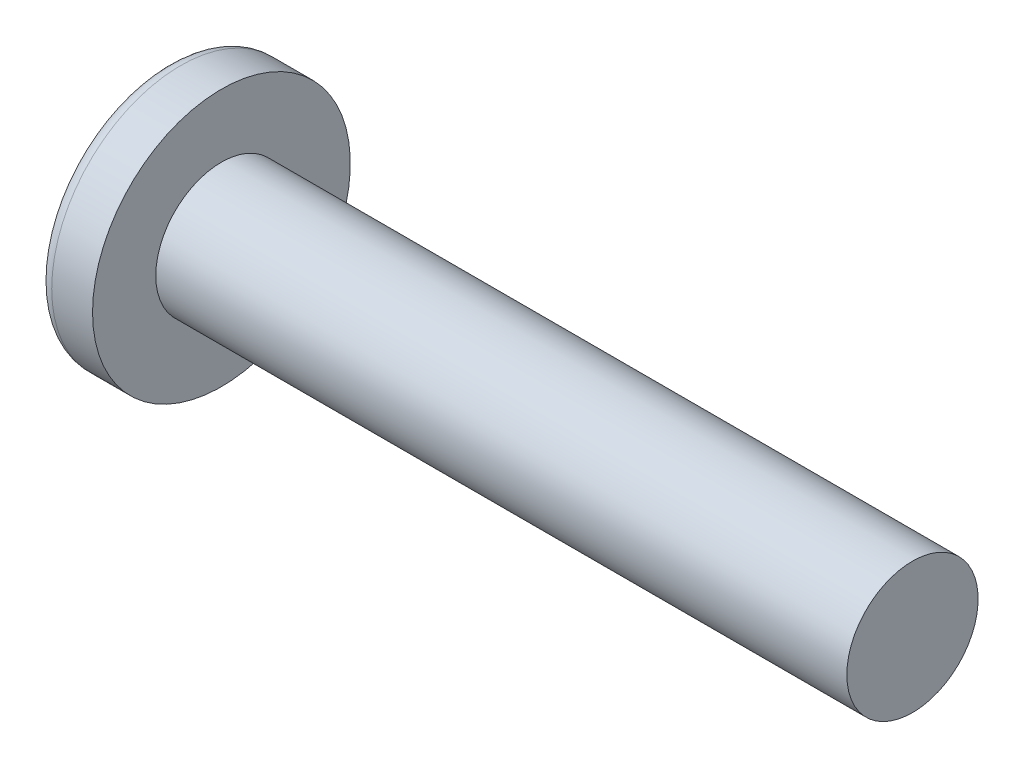
SolidWorks part; units mm, degrees
ref_plane "Plane1" through (0, 0, 0) normal (0, 0, 1) x (1, 0, 0)
ref_plane "Plane2" through (0, 0, 0) normal (0, 1, 0) x (1, 0, 0)
ref_plane "Plane3" through (0, 0, 0) normal (1, 0, 0) x (0, 0, -1)
sketch "BodySke" plane through (0, 0, 0) normal (0, 0, 1) x (1, 0, 0)
  line L0 (3.3782, 2.413) -> (3.3782, 4.7371)
  line L1 (3.9078, 6.35) -> (3.9078, -3.175) construction
  line L2 (-25.4, 0) -> (127, 0) construction
  line L3 (28.7782, 0) -> (0, 0)
  line L4 (3.3782, 2.413) -> (28.7782, 2.413)
  line L5 (28.7782, 2.413) -> (28.7782, 0)
  line L6 (1.8777, 4.7371) -> (3.3782, 4.7371)
  line L7 (3.3782, -2.413) -> (28.7782, -2.413) construction
  line L8 (3.3782, 6.35) -> (3.3782, -3.175) construction
  arc A0 (1.4662, 4.5269) -> (0, 0) centre (7.7216, 0) ccw
  arc A2 (1.4662, 4.5269) -> (1.8777, 4.7371) centre (1.8777, 4.2291) cw
  dimension "Head_crown_rad" = 7.7216
  dimension "Head_fillet_rad" = 0.508
  dimension "Diameter" = 4.826
  dimension "Length" = 25.4
  dimension "Head_ht" = 3.3782
  dimension "Head_dia" = 9.4742
  dimension "Advance" = 1.0592
  dimension "Thread_nom" = 25.4
revolve "Base-Revolve" add sketch "BodySke" angle 360 about L2
cosmetic thread "ThreadCosmetic" [suppressed] parameters "Thread_length"=24.3408, "Thread_minor"=3.5662
sketch "Sketch3" plane through (0, 0, 0) normal (1, 0, 0) x (0, 0, -1)
  line L0 (0.5842, -3.048) -> (-0.5842, -3.048)
  line L1 (0.5842, -3.048) -> (0.5842, 3.048)
  line L2 (-0.5842, 3.048) -> (0.5842, 3.048)
  line L3 (-0.5842, 3.048) -> (-0.5842, -3.048)
  dimension "Cross_dia" = 6.096
  dimension "D1" = 3.048
  dimension "Cross_width" = 1.1684
  dimension "D2" = 0.5842
ref_plane "Plane4" through (3.4798, 0, 0) normal (1, 0, 0) x (0, 0, -1)
sketch "Sketch4" plane through (3.4798, 0, 0) normal (1, 0, 0) x (0, 0, -1)
  line L0 (0.2921, -0.2921) -> (-0.2921, -0.2921)
  line L1 (0.2921, -0.2921) -> (0.2921, 0.2921)
  line L2 (-0.2921, 0.2921) -> (0.2921, 0.2921)
  line L3 (-0.2921, 0.2921) -> (-0.2921, -0.2921)
  dimension "D2" = 0.5842
  dimension "D1" = 0.5842
  dimension "D3" = 0.2921
  dimension "D4" = 0.2921
loft "Cut-Loft1" cut profiles "Sketch3", "Sketch4"
pattern_circular "CirPattern1" count 2 every 90 about axis through (0, 0, 0) along (1, 0, 0) of "Cut-Loft1"
sketch "ThdSchSke" plane through (0, 0, 0) normal (0, 0, 1) x (1, 0, 0)
  line L0 (4.4374, -1.7831) -> (3.9963, -2.413)
  line L1 (4.4374, -1.7831) -> (4.8785, -2.413)
  line L2 (4.8785, -2.413) -> (4.8785, -3.0162)
  line L3 (-3.175, 0) -> (5.1513, 0) construction
  line L5 (4.8785, -3.0162) -> (3.9963, -3.0162)
  line L6 (3.9963, -3.0162) -> (3.9963, -2.413)
  dimension "Diameter" = 4.826
  dimension "SideAngle" = 55
  dimension "VeeAngle" = 70
  dimension "Thread_minor" = 3.5662
  dimension "Overcut" = 6.0325
  dimension "Start" = 4.4374
revolve "ThreadSchematic" [suppressed] cut sketch "ThdSchSke" angle 360 about L3
pattern_linear "ThdSchPat" [suppressed]
equation "\"D1@Sketch3\" = \"Cross_dia@Sketch3\" / 2"
equation "\"D2@Sketch3\" = \"Cross_width@Sketch3\" / 2"
equation "\"D1@Sketch4\" = \"Cross_width@Sketch3\" *.5"
equation "\"D2@Sketch4\" = \"D1@Sketch4\""
equation "\"D3@Sketch4\" = \"D1@Sketch4\" / 2"
equation "\"D4@Sketch4\" = \"D2@Sketch4\" / 2"
equation "\"Thread_length@ThreadCosmetic\" = ((sgn( (\"Length@BodySke\" - \"Advance@BodySke\" ) - \"Thread_nom@BodySke\" )-1)*( (\"Length@BodySke\" - \"Advance@BodySke\" ) - \"Thread_nom@BodySke\" ))/-2+ \"Thread_nom@BodySke\""
equation "\"Thread_minor@ThdSchSke\" = \"Thread_minor@ThreadCosmetic\""
equation "\"Diameter@ThdSchSke\" = \"Diameter@BodySke\""
equation "\"Overcut@ThdSchSke\" = \"Diameter@BodySke\" * 1.25"
equation "\"Start@ThdSchSke\" = \"Head_ht@BodySke\" + \"Length@BodySke\" - \"Thread_length@ThreadCosmetic\"  '---Non-countersunk---"
equation "\"Num_threads@ThdSchPat\" = int( \"Thread_length@ThreadCosmetic\" / \"Advance@BodySke\" + 0.999 )  + 1"
equation "\"Advance@ThdSchPat\" = \"Thread_length@ThreadCosmetic\" /  (\"Num_threads@ThdSchPat\" - 1) 'relax it"
